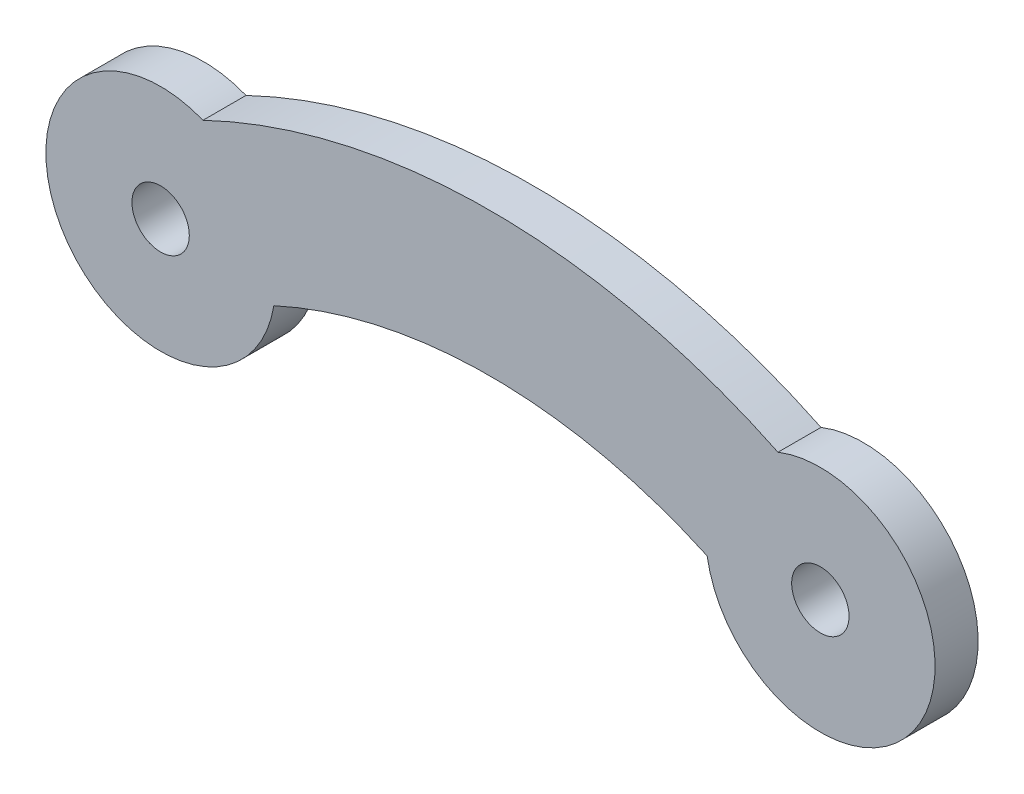
SolidWorks part; units mm, degrees
material "Galvanized Steel"
ref_plane "Front Plane" through (0, 0, 0) normal (0, 0, 1) x (1, 0, 0)
ref_plane "Top Plane" through (0, 0, 0) normal (0, 1, 0) x (1, 0, 0)
ref_plane "Right Plane" through (0, 0, 0) normal (1, 0, 0) x (0, 0, -1)
sketch "Sketch1" plane through (0, 0, 0) normal (0, 0, 1) x (1, 0, 0)
  line L0 (0, 0) -> (23, 0) construction
  line L1 (0, -4) -> (23.0061, -4) construction
  line L2 (11.5031, -4) -> (11.5, 6) construction
  circle A0 centre (0, 0) radius 1
  circle A1 centre (23, 0) radius 1
  arc A2 (1.4774, 3.7172) -> (3.9474, -0.6468) centre (0, 0) ccw
  arc A3 (19.0526, -0.6468) -> (21.5226, 3.7172) centre (23, 0) ccw
  circle A4 centre (0, 0) radius 2.5 construction
  circle A5 centre (23, 0) radius 2.5 construction
  arc A6 (1.4774, 3.7172) -> (21.5226, 3.7172) centre (11.5, -17.1429) cw
  arc A7 (3.9474, -0.6468) -> (19.0526, -0.6468) centre (11.5, -17.1429) cw
  arc A8 (-1.3927, 2.0761) -> (24.5753, 1.9524) centre (11.5, -17.1429) cw construction
  arc A9 (1.3927, -2.0761) -> (21.7504, -2.1731) centre (11.5, -17.1429) cw construction
  point P19 (0, 0)
  dimension "D1" = 2
  dimension "D2" = 2
  dimension "D4" = 8
  dimension "D5" = 8
  dimension "D6" = 5
  dimension "D7" = 5
  dimension "D9" = 5
  dimension "D3" = 23
  dimension "D8" = 10
extrude "Boss-Extrude1" add sketch "Sketch1" along normal blind 1.5
